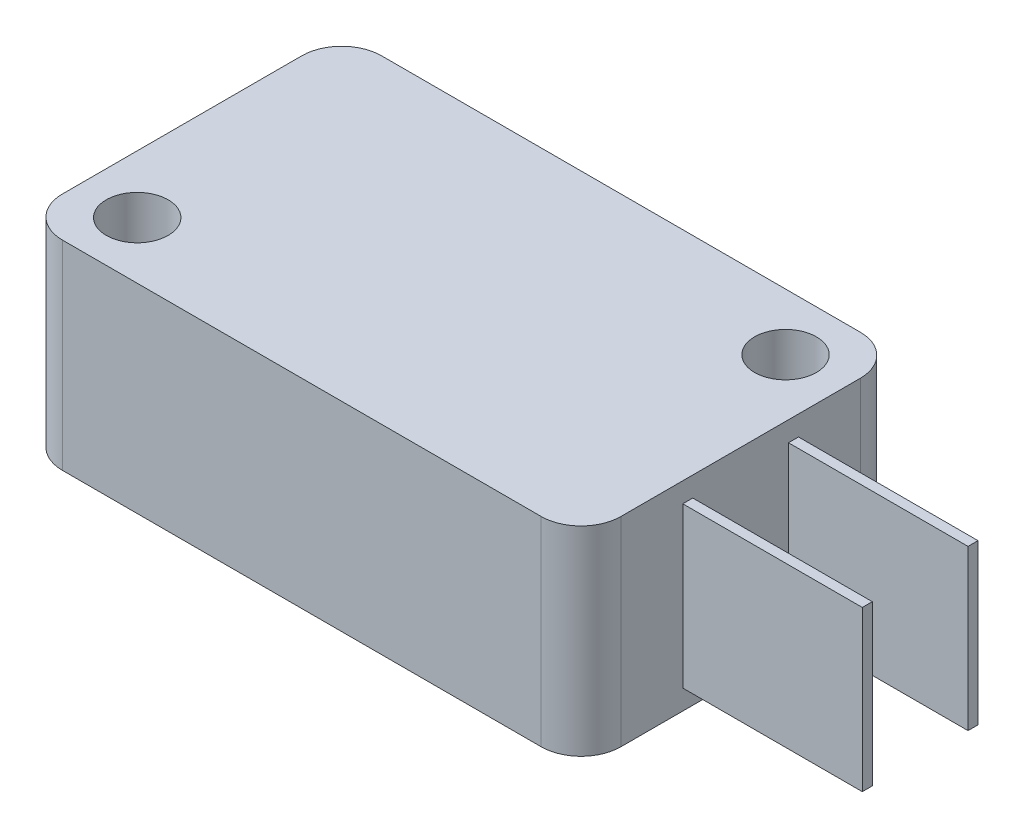
SolidWorks part; units mm, degrees
ref_plane "Front Plane" through (0, 0, 0) normal (0, 0, 1) x (1, 0, 0)
ref_plane "Top Plane" through (0, 0, 0) normal (0, 1, 0) x (1, 0, 0)
ref_plane "Right Plane" through (0, 0, 0) normal (1, 0, 0) x (0, 0, -1)
sketch "스케치1" plane through (0, 0, 0) normal (0, 1, 0) x (1, 0, 0)
  line L1 (-14, 8) -> (14, 8)
  line L2 (-14, 8) -> (-14, -8)
  line L3 (-14, -8) -> (14, -8)
  line L4 (14, 8) -> (14, -8)
  point P7 (-23.4774, 1.7263)
  dimension "D1" = 28
  dimension "D2" = 16
  dimension "D3" = 8
  dimension "D4" = 14
extrude "보스-돌출1" add sketch "스케치1" along normal blind 10
fillet "필렛1" radius 2 4 edges at (-14, 5, -8) (14, 5, -8) (14, 5, 8) (-14, 5, 8)
sketch "스케치2" plane through (0, 10, 0) normal (0, 1, 0) x (1, 0, 0)
  line L0 (11.1, 3.5676) -> (11.1, -49996.4324) construction
  line L1 (-11.1, 2.2245) -> (-11.1, -49997.7755) construction
  line L2 (-8.3663, 5.15) -> (49991.6337, 5.15) construction
  line L3 (-6.2957, -5.15) -> (49993.7043, -5.15) construction
  line L5 (0, 0) -> (0, 50000) construction
  line L9 (0, 0) -> (50000, 0) construction
  circle A0 centre (11.1, 5.15) radius 1.55
  circle A1 centre (-11.1, -5.15) radius 1.55
  dimension "D1" = 11.1
  dimension "D2" = 11.1
  dimension "D3" = 5.15
  dimension "D4" = 5.15
extrude "컷-돌출1" cut sketch "스케치2" against normal blind 10
sketch "스케치3" plane through (14, 0, 0) normal (1, 0, 0) x (0, 0, -1)
  line L0 (0, 0) -> (0, 50000) construction
  line L1 (-6, 10) -> (6, 10) construction
  line L2 (-2.9, 9) -> (-2.4, 9)
  line L3 (-2.9, 9) -> (-2.9, 1)
  line L4 (-2.9, 1) -> (-2.4, 1)
  line L5 (-2.4, 9) -> (-2.4, 1)
  line L6 (2.4, 9) -> (2.9, 9)
  line L7 (2.4, 9) -> (2.4, 1)
  line L8 (2.4, 1) -> (2.9, 1)
  line L9 (2.9, 9) -> (2.9, 1)
  dimension "D1" = 0.5
  dimension "D2" = 0.5
  dimension "D3" = 2.4
  dimension "D4" = 2.4
  dimension "D5" = 8
  dimension "D6" = 8
  dimension "D7" = 1
  dimension "D8" = 1
extrude "보스-돌출2" add sketch "스케치3" along normal blind 9
sketch "스케치4" plane through (0, 0, -8) normal (0, 0, -1) x (-1, 0, 0)
  line L0 (-12, 10) -> (12, 10) construction
  line L1 (4.9656, 6.5) -> (7.9656, 6.5)
  line L2 (4.9656, 6.5) -> (4.9656, 3.5)
  line L3 (4.9656, 3.5) -> (7.9656, 3.5)
  line L4 (7.9656, 6.5) -> (7.9656, 3.5)
  dimension "D1" = 3
  dimension "D2" = 3.5
extrude "보스-돌출3" add sketch "스케치4" along normal blind 2.5
fillet "필렛2" radius 1 2 edges at (-7.9656, 5, -10.5) (-4.9656, 5, -10.5)
